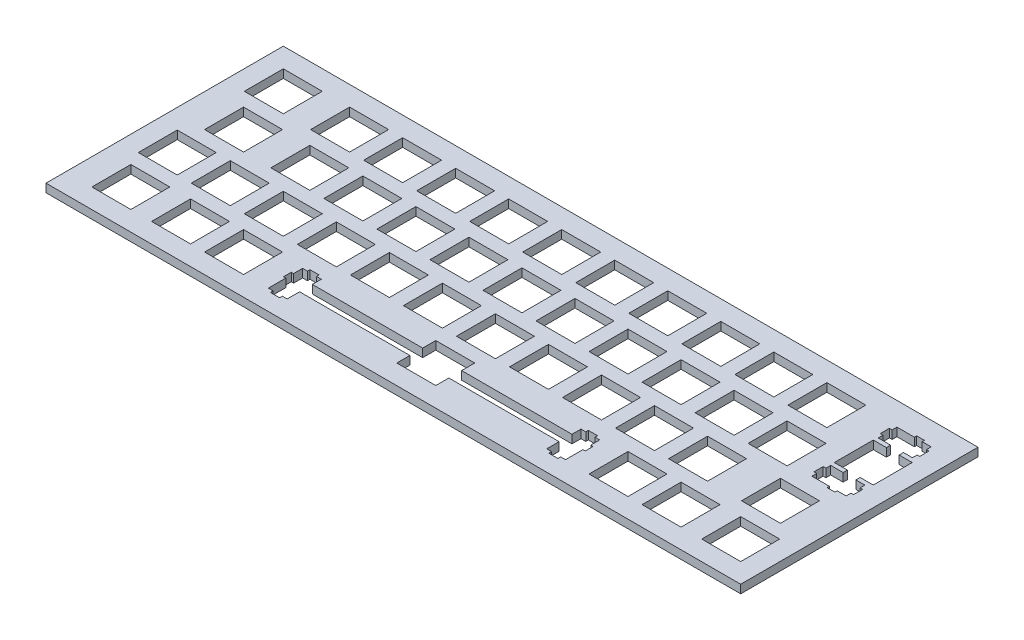
SolidWorks part; units mm, degrees
ref_plane "Plan de face" through (0, 0, 0) normal (0, 0, 1) x (1, 0, 0)
ref_plane "Plan de dessus" through (0, 0, 0) normal (0, 1, 0) x (1, 0, 0)
ref_plane "Plan de droite" through (0, 0, 0) normal (1, 0, 0) x (0, 0, -1)
sketch "Esquisse4" plane through (0, 0, 0) normal (0, 1, 0) x (1, 0, 0)
  line L4 (114.537, 16.7831) -> (114.537, 12.0826)
  line L5 (114.537, 12.0826) -> (74.9131, 12.0826)
  line L6 (74.9131, 12.0826) -> (74.9131, 15.3128)
  line L7 (74.9131, 15.3128) -> (73.1876, 15.3128)
  line L8 (73.1876, 15.3128) -> (73.1876, 16.2347)
  line L9 (73.1876, 16.2347) -> (69.887, 16.2347)
  line L10 (69.887, 16.2347) -> (69.887, 15.3128)
  line L11 (69.887, 15.3128) -> (68.162, 15.3128)
  line L12 (68.162, 15.3128) -> (68.162, 12.0826)
  line L13 (68.162, 12.0826) -> (67.3379, 12.0826)
  line L14 (67.3379, 12.0826) -> (67.3379, 9.2838)
  line L15 (67.3379, 9.2838) -> (68.162, 9.2838)
  line L16 (68.162, 9.2838) -> (68.162, 3.0138)
  line L17 (68.162, 3.0138) -> (69.887, 3.0138)
  line L18 (69.887, 3.0138) -> (69.887, 2.0326)
  line L19 (69.887, 2.0326) -> (73.1876, 2.0326)
  line L20 (73.1876, 2.0326) -> (73.1876, 3.0138)
  line L21 (73.1876, 3.0138) -> (74.9131, 3.0138)
  line L22 (74.9131, 3.0138) -> (74.9131, 7.4827)
  line L23 (74.9131, 7.4827) -> (114.537, 7.4827)
  line L24 (114.537, 7.4827) -> (114.537, 2.7836)
  line L25 (114.537, 2.7836) -> (128.538, 2.7836)
  line L26 (128.538, 2.7836) -> (128.538, 7.4827)
  line L27 (128.538, 7.4827) -> (168.162, 7.4827)
  line L28 (168.162, 7.4827) -> (168.162, 3.0138)
  line L29 (168.162, 3.0138) -> (169.887, 3.0138)
  line L30 (169.887, 3.0138) -> (169.887, 2.0326)
  line L31 (169.887, 2.0326) -> (173.188, 2.0326)
  line L32 (173.188, 2.0326) -> (173.188, 3.0138)
  line L33 (173.188, 3.0138) -> (174.913, 3.0138)
  line L34 (174.913, 3.0138) -> (174.913, 9.2838)
  line L35 (174.913, 9.2838) -> (175.737, 9.2838)
  line L36 (175.737, 9.2838) -> (175.737, 12.0826)
  line L37 (175.737, 12.0826) -> (174.913, 12.0826)
  line L38 (174.913, 12.0826) -> (174.913, 15.3128)
  line L39 (174.913, 15.3128) -> (173.188, 15.3128)
  line L40 (173.188, 15.3128) -> (173.188, 16.2347)
  line L41 (173.188, 16.2347) -> (169.887, 16.2347)
  line L42 (169.887, 16.2347) -> (169.887, 15.3128)
  line L43 (169.887, 15.3128) -> (168.162, 15.3128)
  line L44 (168.162, 15.3128) -> (168.162, 12.0826)
  line L45 (168.162, 12.0826) -> (128.538, 12.0826)
  line L46 (128.538, 12.0826) -> (128.538, 16.7831)
  line L47 (128.538, 16.7831) -> (114.537, 16.7831)
  line L48 (224.076, 16.7831) -> (238.075, 16.7831)
  line L49 (238.075, 16.7831) -> (238.075, 2.7836)
  line L50 (238.075, 2.7836) -> (224.076, 2.7836)
  line L51 (224.076, 2.7836) -> (224.076, 16.7831)
  line L52 (202.645, 16.7831) -> (216.644, 16.7831)
  line L53 (216.644, 16.7831) -> (216.644, 2.7836)
  line L54 (216.644, 2.7836) -> (202.645, 2.7836)
  line L55 (202.645, 2.7836) -> (202.645, 16.7831)
  line L56 (183.595, 16.7831) -> (197.594, 16.7831)
  line L57 (197.594, 16.7831) -> (197.594, 2.7836)
  line L58 (197.594, 2.7836) -> (183.595, 2.7836)
  line L59 (183.595, 2.7836) -> (183.595, 16.7831)
  line L60 (45.4822, 16.7831) -> (59.4815, 16.7831)
  line L61 (59.4815, 16.7831) -> (59.4815, 2.7836)
  line L62 (59.4815, 2.7836) -> (45.4822, 2.7836)
  line L63 (45.4822, 2.7836) -> (45.4822, 16.7831)
  line L64 (26.4322, 16.7831) -> (40.4315, 16.7831)
  line L65 (40.4315, 16.7831) -> (40.4315, 2.7836)
  line L66 (40.4315, 2.7836) -> (26.4322, 2.7836)
  line L67 (26.4322, 2.7836) -> (26.4322, 16.7831)
  line L68 (5.0009, 16.7831) -> (19.0004, 16.7831)
  line L69 (19.0004, 16.7831) -> (19.0004, 2.7836)
  line L70 (19.0004, 2.7836) -> (5.0009, 2.7836)
  line L71 (5.0009, 2.7836) -> (5.0009, 16.7831)
  line L72 (219.312, 35.833) -> (233.313, 35.833)
  line L73 (233.313, 35.833) -> (233.313, 21.8336)
  line L74 (233.313, 21.8336) -> (219.312, 21.8336)
  line L75 (219.312, 21.8336) -> (219.312, 35.833)
  line L76 (193.12, 35.833) -> (207.119, 35.833)
  line L77 (207.119, 35.833) -> (207.119, 21.8336)
  line L78 (207.119, 21.8336) -> (193.12, 21.8336)
  line L79 (193.12, 21.8336) -> (193.12, 35.833)
  line L80 (174.07, 35.833) -> (188.069, 35.833)
  line L81 (188.069, 35.833) -> (188.069, 21.8336)
  line L82 (188.069, 21.8336) -> (174.07, 21.8336)
  line L83 (174.07, 21.8336) -> (174.07, 35.833)
  line L84 (155.02, 35.833) -> (169.019, 35.833)
  line L85 (169.019, 35.833) -> (169.019, 21.8336)
  line L86 (169.019, 21.8336) -> (155.02, 21.8336)
  line L87 (155.02, 21.8336) -> (155.02, 35.833)
  line L88 (135.97, 35.833) -> (149.969, 35.833)
  line L89 (149.969, 35.833) -> (149.969, 21.8336)
  line L90 (149.969, 21.8336) -> (135.97, 21.8336)
  line L91 (135.97, 21.8336) -> (135.97, 35.833)
  line L92 (116.918, 35.833) -> (130.919, 35.833)
  line L93 (130.919, 35.833) -> (130.919, 21.8336)
  line L94 (130.919, 21.8336) -> (116.918, 21.8336)
  line L95 (116.918, 21.8336) -> (116.918, 35.833)
  line L96 (97.8683, 35.833) -> (111.869, 35.833)
  line L97 (111.869, 35.833) -> (111.869, 21.8336)
  line L98 (111.869, 21.8336) -> (97.8683, 21.8336)
  line L99 (97.8683, 21.8336) -> (97.8683, 35.833)
  line L100 (78.8197, 35.833) -> (92.819, 35.833)
  line L101 (92.819, 35.833) -> (92.819, 21.8336)
  line L102 (92.819, 21.8336) -> (78.8197, 21.8336)
  line L103 (78.8197, 21.8336) -> (78.8197, 35.833)
  line L104 (59.7697, 35.833) -> (73.769, 35.833)
  line L105 (73.769, 35.833) -> (73.769, 21.8336)
  line L106 (73.769, 21.8336) -> (59.7697, 21.8336)
  line L107 (59.7697, 21.8336) -> (59.7697, 35.833)
  line L108 (40.7197, 35.833) -> (54.719, 35.833)
  line L109 (54.719, 35.833) -> (54.719, 21.8336)
  line L110 (54.719, 21.8336) -> (40.7197, 21.8336)
  line L111 (40.7197, 21.8336) -> (40.7197, 35.833)
  line L112 (21.6697, 35.833) -> (35.669, 35.833)
  line L113 (35.669, 35.833) -> (35.669, 21.8336)
  line L114 (35.669, 21.8336) -> (21.6697, 21.8336)
  line L115 (21.6697, 21.8336) -> (21.6697, 35.833)
  line L116 (2.6197, 35.833) -> (16.6192, 35.833)
  line L117 (16.6192, 35.833) -> (16.6192, 21.8336)
  line L118 (16.6192, 21.8336) -> (2.6197, 21.8336)
  line L119 (2.6197, 21.8336) -> (2.6197, 35.833)
  line L120 (202.645, 54.8831) -> (216.644, 54.8831)
  line L121 (216.644, 54.8831) -> (216.644, 40.8838)
  line L122 (216.644, 40.8838) -> (202.645, 40.8838)
  line L123 (202.645, 40.8838) -> (202.645, 54.8831)
  line L124 (183.595, 54.8831) -> (197.594, 54.8831)
  line L125 (197.594, 54.8831) -> (197.594, 40.8838)
  line L126 (197.594, 40.8838) -> (183.595, 40.8838)
  line L127 (183.595, 40.8838) -> (183.595, 54.8831)
  line L128 (164.545, 54.8831) -> (178.544, 54.8831)
  line L129 (178.544, 54.8831) -> (178.544, 40.8838)
  line L130 (178.544, 40.8838) -> (164.545, 40.8838)
  line L131 (164.545, 40.8838) -> (164.545, 54.8831)
  line L132 (145.495, 54.8831) -> (159.494, 54.8831)
  line L133 (159.494, 54.8831) -> (159.494, 40.8838)
  line L134 (159.494, 40.8838) -> (145.495, 40.8838)
  line L135 (145.495, 40.8838) -> (145.495, 54.8831)
  line L136 (126.445, 54.8831) -> (140.444, 54.8831)
  line L137 (140.444, 54.8831) -> (140.444, 40.8838)
  line L138 (140.444, 40.8838) -> (126.445, 40.8838)
  line L139 (126.445, 40.8838) -> (126.445, 54.8831)
  line L140 (107.395, 54.8831) -> (121.394, 54.8831)
  line L141 (121.394, 54.8831) -> (121.394, 40.8838)
  line L142 (121.394, 40.8838) -> (107.395, 40.8838)
  line L143 (107.395, 40.8838) -> (107.395, 54.8831)
  line L144 (88.3447, 54.8831) -> (102.344, 54.8831)
  line L145 (102.344, 54.8831) -> (102.344, 40.8838)
  line L146 (102.344, 40.8838) -> (88.3447, 40.8838)
  line L147 (88.3447, 40.8838) -> (88.3447, 54.8831)
  line L148 (69.2947, 54.8831) -> (83.294, 54.8831)
  line L149 (83.294, 54.8831) -> (83.294, 40.8838)
  line L150 (83.294, 40.8838) -> (69.2947, 40.8838)
  line L151 (69.2947, 40.8838) -> (69.2947, 54.8831)
  line L152 (50.2447, 54.8831) -> (64.244, 54.8831)
  line L153 (64.244, 54.8831) -> (64.244, 40.8838)
  line L154 (64.244, 40.8838) -> (50.2447, 40.8838)
  line L155 (50.2447, 40.8838) -> (50.2447, 54.8831)
  line L156 (31.1947, 54.8831) -> (45.194, 54.8831)
  line L157 (45.194, 54.8831) -> (45.194, 40.8838)
  line L158 (45.194, 40.8838) -> (31.1947, 40.8838)
  line L159 (31.1947, 40.8838) -> (31.1947, 54.8831)
  line L160 (7.3822, 54.8831) -> (21.3817, 54.8831)
  line L161 (21.3817, 54.8831) -> (21.3817, 40.8838)
  line L162 (21.3817, 40.8838) -> (7.3822, 40.8838)
  line L163 (7.3822, 40.8838) -> (7.3822, 54.8831)
  line L164 (230.576, 73.5087) -> (230.576, 72.6832)
  line L165 (230.576, 72.6832) -> (224.306, 72.6832)
  line L166 (224.306, 72.6832) -> (224.306, 70.9581)
  line L167 (224.306, 70.9581) -> (223.325, 70.9581)
  line L168 (223.325, 70.9581) -> (223.325, 67.6589)
  line L169 (223.325, 67.6589) -> (224.306, 67.6589)
  line L170 (224.306, 67.6589) -> (224.306, 65.9335)
  line L171 (224.306, 65.9335) -> (228.775, 65.9335)
  line L172 (228.775, 65.9335) -> (228.775, 64.4081)
  line L173 (228.775, 64.4081) -> (224.076, 64.4081)
  line L174 (224.076, 64.4081) -> (224.076, 50.4088)
  line L175 (224.076, 50.4088) -> (228.775, 50.4088)
  line L176 (228.775, 50.4088) -> (228.775, 48.883)
  line L177 (228.775, 48.883) -> (224.306, 48.883)
  line L178 (224.306, 48.883) -> (224.306, 47.1579)
  line L179 (224.306, 47.1579) -> (223.325, 47.1579)
  line L180 (223.325, 47.1579) -> (223.325, 43.8587)
  line L181 (223.325, 43.8587) -> (224.306, 43.8587)
  line L182 (224.306, 43.8587) -> (224.306, 42.1337)
  line L183 (224.306, 42.1337) -> (230.576, 42.1337)
  line L184 (230.576, 42.1337) -> (230.576, 41.3082)
  line L185 (230.576, 41.3082) -> (233.375, 41.3082)
  line L186 (233.375, 41.3082) -> (233.375, 42.1337)
  line L187 (233.375, 42.1337) -> (236.605, 42.1337)
  line L188 (236.605, 42.1337) -> (236.605, 43.8587)
  line L189 (236.605, 43.8587) -> (237.526, 43.8587)
  line L190 (237.526, 43.8587) -> (237.526, 47.1579)
  line L191 (237.526, 47.1579) -> (236.605, 47.1579)
  line L192 (236.605, 47.1579) -> (236.605, 48.883)
  line L193 (236.605, 48.883) -> (233.375, 48.883)
  line L194 (233.375, 48.883) -> (233.375, 50.4088)
  line L195 (233.375, 50.4088) -> (238.075, 50.4088)
  line L196 (238.075, 50.4088) -> (238.075, 64.4081)
  line L197 (238.075, 64.4081) -> (233.375, 64.4081)
  line L198 (233.375, 64.4081) -> (233.375, 65.9335)
  line L199 (233.375, 65.9335) -> (236.605, 65.9335)
  line L200 (236.605, 65.9335) -> (236.605, 67.6589)
  line L201 (236.605, 67.6589) -> (237.526, 67.6589)
  line L202 (237.526, 67.6589) -> (237.526, 70.9581)
  line L203 (237.526, 70.9581) -> (236.605, 70.9581)
  line L204 (236.605, 70.9581) -> (236.605, 72.6832)
  line L205 (236.605, 72.6832) -> (233.375, 72.6832)
  line L206 (233.375, 72.6832) -> (233.375, 73.5087)
  line L207 (233.375, 73.5087) -> (230.576, 73.5087)
  line L208 (197.882, 73.9331) -> (211.882, 73.9331)
  line L209 (211.882, 73.9331) -> (211.882, 59.9338)
  line L210 (211.882, 59.9338) -> (197.882, 59.9338)
  line L211 (197.882, 59.9338) -> (197.882, 73.9331)
  line L212 (178.832, 73.9331) -> (192.832, 73.9331)
  line L213 (192.832, 73.9331) -> (192.832, 59.9338)
  line L214 (192.832, 59.9338) -> (178.832, 59.9338)
  line L215 (178.832, 59.9338) -> (178.832, 73.9331)
  line L216 (159.782, 73.9331) -> (173.782, 73.9331)
  line L217 (173.782, 73.9331) -> (173.782, 59.9338)
  line L218 (173.782, 59.9338) -> (159.782, 59.9338)
  line L219 (159.782, 59.9338) -> (159.782, 73.9331)
  line L220 (140.732, 73.9331) -> (154.732, 73.9331)
  line L221 (154.732, 73.9331) -> (154.732, 59.9338)
  line L222 (154.732, 59.9338) -> (140.732, 59.9338)
  line L223 (140.732, 59.9338) -> (140.732, 73.9331)
  line L224 (121.682, 73.9331) -> (135.682, 73.9331)
  line L225 (135.682, 73.9331) -> (135.682, 59.9338)
  line L226 (135.682, 59.9338) -> (121.682, 59.9338)
  line L227 (121.682, 59.9338) -> (121.682, 73.9331)
  line L228 (102.632, 73.9331) -> (116.632, 73.9331)
  line L229 (116.632, 73.9331) -> (116.632, 59.9338)
  line L230 (116.632, 59.9338) -> (102.632, 59.9338)
  line L231 (102.632, 59.9338) -> (102.632, 73.9331)
  line L232 (83.5822, 73.9331) -> (97.5815, 73.9331)
  line L233 (97.5815, 73.9331) -> (97.5815, 59.9338)
  line L234 (97.5815, 59.9338) -> (83.5822, 59.9338)
  line L235 (83.5822, 59.9338) -> (83.5822, 73.9331)
  line L236 (64.5322, 73.9331) -> (78.5315, 73.9331)
  line L237 (78.5315, 73.9331) -> (78.5315, 59.9338)
  line L238 (78.5315, 59.9338) -> (64.5322, 59.9338)
  line L239 (64.5322, 59.9338) -> (64.5322, 73.9331)
  line L240 (45.4822, 73.9331) -> (59.4815, 73.9331)
  line L241 (59.4815, 73.9331) -> (59.4815, 59.9338)
  line L242 (59.4815, 59.9338) -> (45.4822, 59.9338)
  line L243 (45.4822, 59.9338) -> (45.4822, 73.9331)
  line L244 (26.4322, 73.9331) -> (40.4315, 73.9331)
  line L245 (40.4315, 73.9331) -> (40.4315, 59.9338)
  line L246 (40.4315, 59.9338) -> (26.4322, 59.9338)
  line L247 (26.4322, 59.9338) -> (26.4322, 73.9331)
  line L248 (2.6197, 73.9331) -> (16.6192, 73.9331)
  line L249 (16.6192, 73.9331) -> (16.6192, 59.9338)
  line L250 (16.6192, 59.9338) -> (2.6197, 59.9338)
  line L251 (2.6197, 59.9338) -> (2.6197, 73.9331)
  line L253 (-4.4303, 80.9831) -> (245.125, 80.9831)
  line L254 (-4.4303, 80.9831) -> (-4.4303, -4.2664)
  line L255 (-4.4303, -4.2664) -> (245.125, -4.2664)
  line L256 (245.125, 80.9831) -> (245.125, -4.2664)
  dimension "D1" = 7.05
  dimension "D2" = 13.9995
  dimension "D3" = 13.9993
  dimension "D4" = 7.05
  dimension "D5" = 13.9995
  dimension "D6" = 13.999
  dimension "D7" = 7.05
  dimension "D8" = 7.05
extrude "Boss.-Extru.2" add sketch "Esquisse4" along normal blind 3
